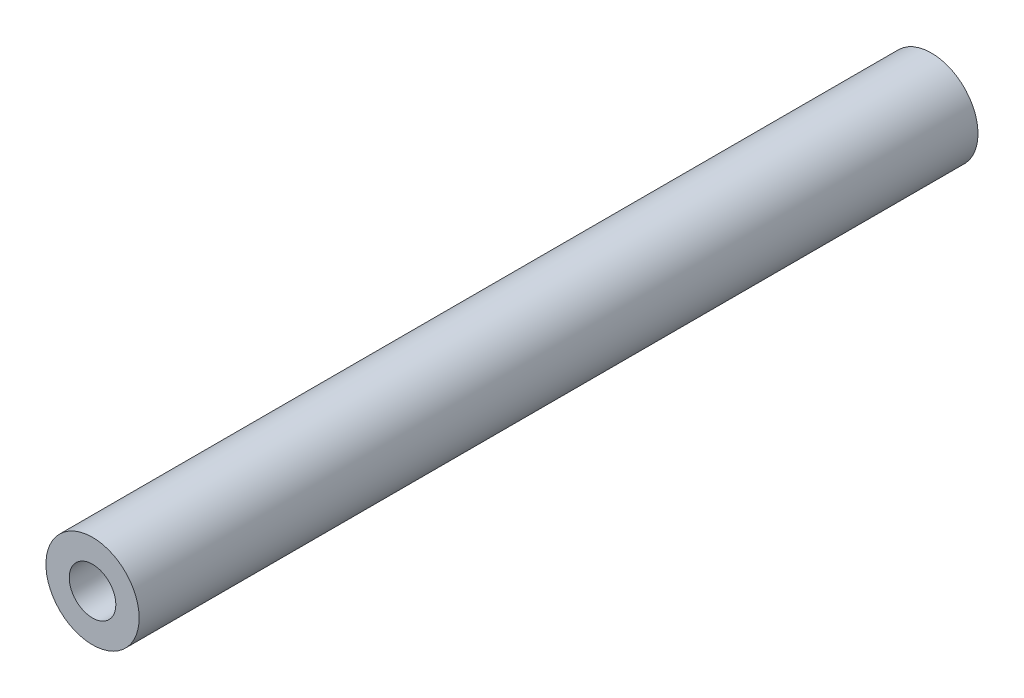
SolidWorks part; units mm, degrees
ref_plane "Plan de face" through (0, 0, 0) normal (0, 0, 1) x (1, 0, 0)
ref_plane "Plan de dessus" through (0, 0, 0) normal (0, 1, 0) x (1, 0, 0)
ref_plane "Plan de droite" through (0, 0, 0) normal (1, 0, 0) x (0, 0, -1)
sketch "Esquisse1" plane through (0, 0, 0) normal (0, 0, 1) x (1, 0, 0)
  circle A0 centre (0, 0) radius 1.25
  circle A1 centre (0, 0) radius 2.5
  dimension "D1" = 2.5
  dimension "D2" = 5
extrude "Boss.-Extru.1" add sketch "Esquisse1" along normal blind 45
